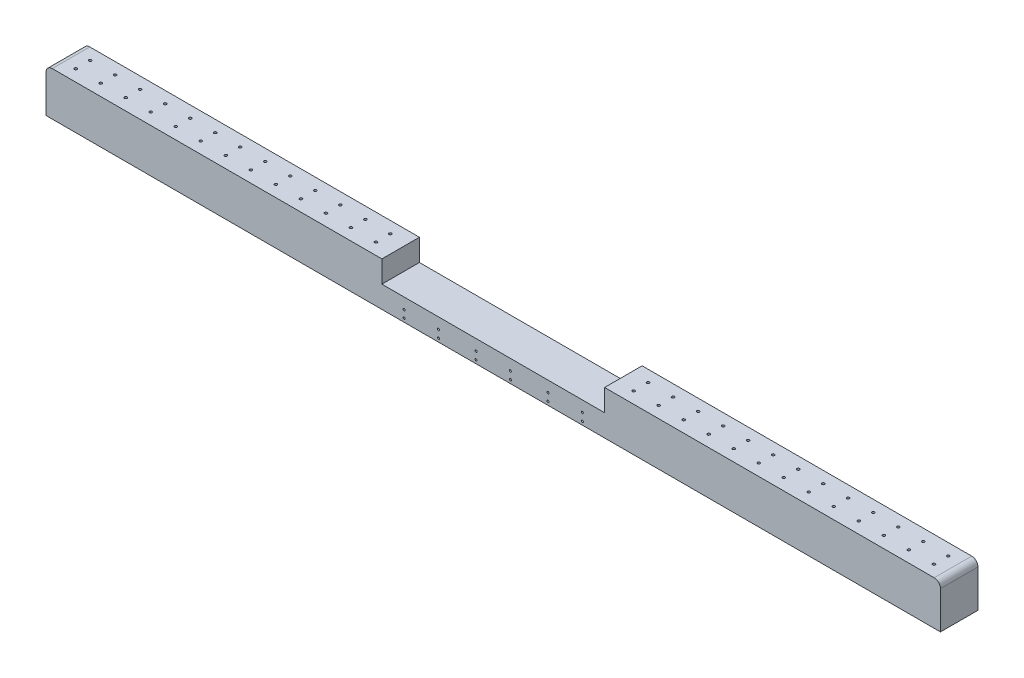
SolidWorks part; units mm, degrees
material "201 Annealed Stainless Steel (SS)"
ref_plane "Front Plane" through (0, 0, 0) normal (0, 0, 1) x (1, 0, 0)
ref_plane "Top Plane" through (0, 0, 0) normal (0, 1, 0) x (1, 0, 0)
ref_plane "Right Plane" through (0, 0, 0) normal (1, 0, 0) x (0, 0, -1)
sketch "Sketch1" plane through (0, 0, 0) normal (0, 1, 0) x (1, 0, 0)
  line L1 (715, -30) -> (-715, -30)
  line L2 (715, -30) -> (715, 30)
  line L3 (715, 30) -> (-715, 30)
  line L4 (-715, -30) -> (-715, 30)
  line L5 (715, -30) -> (-715, 30) construction
  line L6 (715, 30) -> (-715, -30) construction
  point P0 (0, 0)
  dimension "D1" = 1430
  dimension "D2" = 60
extrude "Boss-Extrude1" add sketch "Sketch1" along normal mid plane 70
sketch "Sketch2" plane through (0, 35, 0) normal (0, 1, 0) x (1, 0, 0)
  line L0 (0, -30) -> (0, 30) construction
  line L1 (715, 30) -> (-715, 30) construction
  line L3 (178, -30) -> (-178, -30)
  line L4 (178, -30) -> (178, 30)
  line L5 (178, 30) -> (-178, 30)
  line L6 (-178, -30) -> (-178, 30)
  line L7 (178, -30) -> (-178, 30) construction
  line L8 (178, 30) -> (-178, -30) construction
  point P0 (0, 0)
  point P6 (0, 0)
  dimension "D1" = 356
extrude "Cut-Extrude1" cut sketch "Sketch2" against normal blind 35
sketch "Sketch3" plane through (0, 35, 0) normal (0, 1, 0) x (1, 0, 0)
  point P0 (205.9918, -11.5)
  point P1 (205.9918, 11.5)
  point P3 (245.9918, 11.5)
  point P5 (245.9918, -11.5)
hole_wizard "M5x0.8 Tapped Hole2" positions "Sketch6" profile "Sketch7" tap size "M5x0.8" standard "ANSI Metric" end condition through all
sketch "Sketch6" plane through (0, 35, 0) normal (0, 1, 0) x (1, 0, 0)
  point P0 (205.9918, 11.5)
  point P3 (205.9918, -11.5)
sketch "Sketch7" plane through (205.9918, 35, -11.5) normal (1, 0, 0) x (0, 0, 1)
  line L0 (0, 0) -> (0, 70)
  line L1 (0, 70) -> (2.1, 70)
  line L2 (2.1, 70) -> (2.1, 0)
  line L5 (2.1, 0) -> (0, 0)
  line L11 (0, -6.35) -> (0, 107.95) construction
  dimension "Thru Tap Drill Dia." = 4.2
  dimension "Thru Tap Drill Depth" = 70
cosmetic thread "Hole Thread5" parameters "D2"=5
cosmetic thread "Hole Thread6" parameters "D2"=5
pattern_linear "LPattern1" count 13 spacing 40 along (1, 0, 0) of "M5x0.8 Tapped Hole2"
cosmetic thread "Hole Thread7" parameters "D2"=5
cosmetic thread "Hole Thread8" parameters "D2"=5
cosmetic thread "Hole Thread9" parameters "D2"=5
cosmetic thread "Hole Thread10" parameters "D2"=5
cosmetic thread "Hole Thread11" parameters "D2"=5
cosmetic thread "Hole Thread12" parameters "D2"=5
cosmetic thread "Hole Thread13" parameters "D2"=5
cosmetic thread "Hole Thread14" parameters "D2"=5
cosmetic thread "Hole Thread15" parameters "D2"=5
cosmetic thread "Hole Thread16" parameters "D2"=5
cosmetic thread "Hole Thread17" parameters "D2"=5
cosmetic thread "Hole Thread18" parameters "D2"=5
cosmetic thread "Hole Thread19" parameters "D2"=5
cosmetic thread "Hole Thread20" parameters "D2"=5
cosmetic thread "Hole Thread21" parameters "D2"=5
cosmetic thread "Hole Thread22" parameters "D2"=5
cosmetic thread "Hole Thread23" parameters "D2"=5
cosmetic thread "Hole Thread24" parameters "D2"=5
cosmetic thread "Hole Thread25" parameters "D2"=5
cosmetic thread "Hole Thread26" parameters "D2"=5
cosmetic thread "Hole Thread27" parameters "D2"=5
cosmetic thread "Hole Thread28" parameters "D2"=5
cosmetic thread "Hole Thread29" parameters "D2"=5
cosmetic thread "Hole Thread30" parameters "D2"=5
mirror "Mirror1" about plane through (0, 0, 0) normal (1, 0, 0) of "LPattern1", "M5x0.8 Tapped Hole2"
cosmetic thread "Hole Thread31" parameters "D2"=5
cosmetic thread "Hole Thread32" parameters "D2"=5
cosmetic thread "Hole Thread33" parameters "D2"=5
cosmetic thread "Hole Thread34" parameters "D2"=5
cosmetic thread "Hole Thread35" parameters "D2"=5
cosmetic thread "Hole Thread36" parameters "D2"=5
cosmetic thread "Hole Thread37" parameters "D2"=5
cosmetic thread "Hole Thread38" parameters "D2"=5
cosmetic thread "Hole Thread39" parameters "D2"=5
cosmetic thread "Hole Thread40" parameters "D2"=5
cosmetic thread "Hole Thread41" parameters "D2"=5
cosmetic thread "Hole Thread42" parameters "D2"=5
cosmetic thread "Hole Thread43" parameters "D2"=5
cosmetic thread "Hole Thread44" parameters "D2"=5
cosmetic thread "Hole Thread45" parameters "D2"=5
cosmetic thread "Hole Thread46" parameters "D2"=5
cosmetic thread "Hole Thread47" parameters "D2"=5
cosmetic thread "Hole Thread48" parameters "D2"=5
cosmetic thread "Hole Thread49" parameters "D2"=5
cosmetic thread "Hole Thread50" parameters "D2"=5
cosmetic thread "Hole Thread51" parameters "D2"=5
cosmetic thread "Hole Thread52" parameters "D2"=5
cosmetic thread "Hole Thread53" parameters "D2"=5
cosmetic thread "Hole Thread54" parameters "D2"=5
cosmetic thread "Hole Thread55" parameters "D2"=5
cosmetic thread "Hole Thread56" parameters "D2"=5
sketch "Sketch8" plane through (0, 0, 30) normal (0, 0, 1) x (1, 0, 0)
  point P0 (142.5, -17.5)
  point P1 (142.5, -29.5)
  point P3 (87.5, -29.5)
  point P5 (87.5, -17.5)
  point P7 (27.5, -17.5)
  point P9 (27.5, -29.5)
hole_wizard "M4x0.7 Tapped Hole1" positions "Sketch9" profile "Sketch10" tap size "M4x0.7" standard "ANSI Metric"
sketch "Sketch9" plane through (0, 0, 30) normal (0, 0, 1) x (1, 0, 0)
  point P0 (142.5, -17.5)
  point P3 (142.5, -29.5)
  point P6 (87.5, -17.5)
  point P9 (87.5, -29.5)
  point P12 (27.5, -17.5)
  point P15 (27.5, -29.5)
sketch "Sketch10" plane through (142.5, -17.5, 30) normal (1, 0, 0) x (0, -1, 0)
  line L0 (0, 0) -> (0, 15.9914)
  line L1 (0, 15.9914) -> (1.65, 15)
  line L2 (1.65, 15) -> (1.65, 0)
  line L5 (1.65, 0) -> (0, 0)
  line L10 (0, 15.9914) -> (-1.65, 15) construction
  line L11 (0, -6.35) -> (0, 107.95) construction
  dimension "Tap Drill Dia." = 3.3
  dimension "Tap Drill Depth" = 15
  dimension "Drill Angle" = 118
cosmetic thread "Hole Thread57" parameters "D1"=8, "D2"=4
cosmetic thread "Hole Thread58" parameters "D1"=8, "D2"=4
cosmetic thread "Hole Thread59" parameters "D1"=8, "D2"=4
cosmetic thread "Hole Thread60" parameters "D1"=8, "D2"=4
cosmetic thread "Hole Thread61" parameters "D1"=8, "D2"=4
cosmetic thread "Hole Thread62" parameters "D1"=8, "D2"=4
mirror "Mirror2" about plane through (0, 0, 0) normal (1, 0, 0) of "M4x0.7 Tapped Hole1"
cosmetic thread "Hole Thread63" parameters "D1"=8, "D2"=4
cosmetic thread "Hole Thread64" parameters "D1"=8, "D2"=4
cosmetic thread "Hole Thread65" parameters "D1"=8, "D2"=4
cosmetic thread "Hole Thread66" parameters "D1"=8, "D2"=4
cosmetic thread "Hole Thread67" parameters "D1"=8, "D2"=4
cosmetic thread "Hole Thread68" parameters "D1"=8, "D2"=4
mirror "Mirror3" about plane through (0, 0, 0) normal (0, 0, 1) of "Mirror2", "M4x0.7 Tapped Hole1"
cosmetic thread "Hole Thread69" parameters "D1"=8, "D2"=4
cosmetic thread "Hole Thread70" parameters "D1"=8, "D2"=4
cosmetic thread "Hole Thread71" parameters "D1"=8, "D2"=4
cosmetic thread "Hole Thread72" parameters "D1"=8, "D2"=4
cosmetic thread "Hole Thread73" parameters "D1"=8, "D2"=4
cosmetic thread "Hole Thread74" parameters "D1"=8, "D2"=4
cosmetic thread "Hole Thread75" parameters "D1"=8, "D2"=4
cosmetic thread "Hole Thread76" parameters "D1"=8, "D2"=4
cosmetic thread "Hole Thread77" parameters "D1"=8, "D2"=4
cosmetic thread "Hole Thread78" parameters "D1"=8, "D2"=4
cosmetic thread "Hole Thread79" parameters "D1"=8, "D2"=4
cosmetic thread "Hole Thread80" parameters "D1"=8, "D2"=4
fillet "Fillet1" radius 10 2 edges at (-715, 35, 0) (715, 35, 0)
